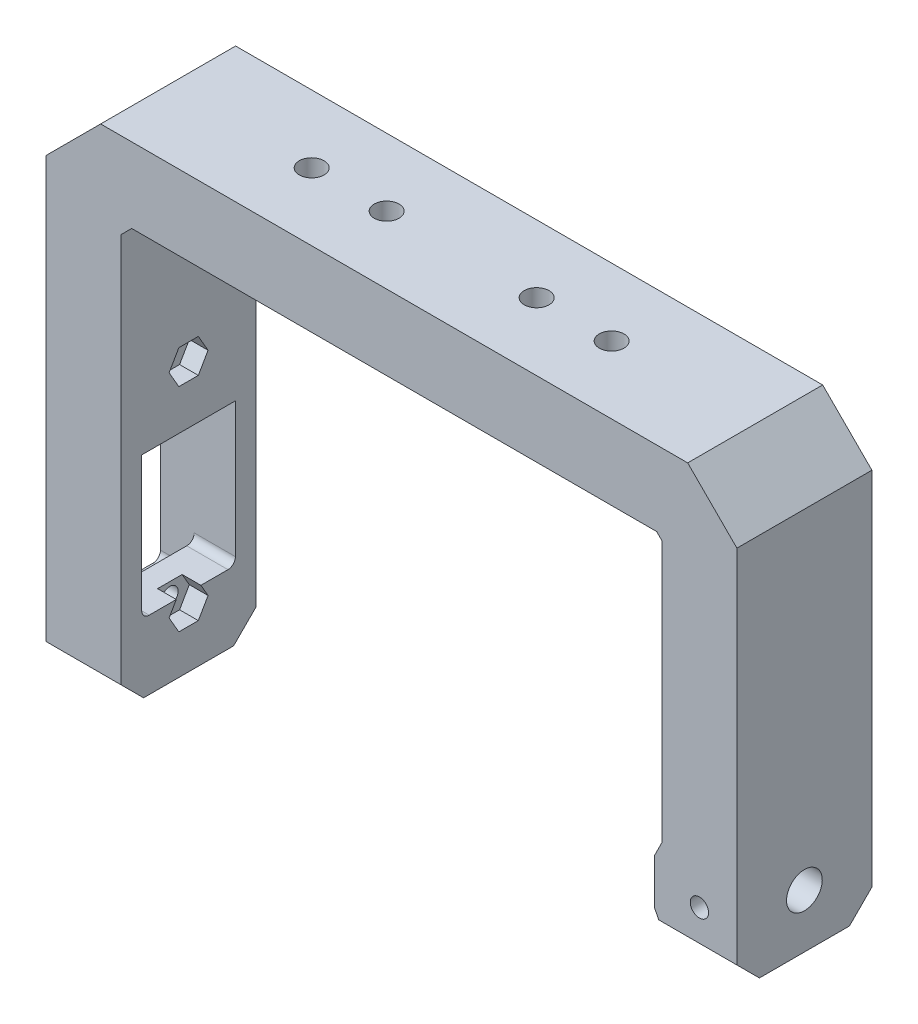
SolidWorks part; units mm, degrees
ref_plane "Front" through (0, 0, 0) normal (0, 0, 1) x (1, 0, 0)
ref_plane "Top" through (0, 0, 0) normal (0, 1, 0) x (1, 0, 0)
ref_plane "Right" through (0, 0, 0) normal (1, 0, 0) x (0, 0, -1)
sketch "Sketch1" plane through (0, 0, 0) normal (0, 0, 1) x (1, 0, 0)
  line L0 (-35, 0) -> (35, 0)
  line L1 (-35, 0) -> (-36.4142, -1.4142)
  line L2 (35, 0) -> (35.7071, -0.7071)
  line L3 (-36.4142, -1.4142) -> (-36.4142, -56.4142)
  line L4 (35.7071, -0.7071) -> (35.7071, -47.7071)
  line L5 (45.7071, 3.435) -> (45.7071, -47.7071)
  line L6 (39.1421, 10) -> (45.7071, 3.435)
  line L7 (-39.1421, 10) -> (39.1421, 10)
  line L8 (-39.1421, 10) -> (-46.4142, 2.7279)
  line L9 (-46.4142, 2.7279) -> (-46.4142, -56.4142)
  line L10 (-36.4142, -56.4142) -> (-46.4142, -56.4142)
  line L11 (35.7071, -47.7071) -> (45.7071, -47.7071)
  point P4 (0, 0)
  dimension "D1" = 70
  dimension "D2" = 2
  dimension "D3" = 1
  dimension "D4" = 55
  dimension "D5" = 47
  dimension "D6" = 45
  dimension "D7" = 10
extrude "Boss-Extrude1" add sketch "Sketch1" along normal mid plane 18
sketch "Sketch2" plane through (0, 10, 0) normal (0, 1, 0) x (1, 0, 0)
  line L0 (-39.1421, 0) -> (39.1421, 0) construction
  line L1 (39.1421, -9) -> (39.1421, 9) construction
  circle A0 centre (-10, 0) radius 0.5
  circle A1 centre (10, 0) radius 0.5
  circle A2 centre (-20, 0) radius 0.5
  circle A3 centre (20, 0) radius 0.5
  point P6 (0, 0)
  dimension "D1" = 1
  dimension "D2" = 1
  dimension "D5" = 1
  dimension "D6" = 1
  dimension "D3" = 10
  dimension "D4" = 10
  dimension "D7" = 20
  dimension "D8" = 20
extrude "Cut-Extrude1" cut sketch "Sketch2" against normal through all contours A0 | A1 | A2 | A3
sketch "Sketch9" plane through (45.7071, 0, 0) normal (1, 0, 0) x (0, 0, -1)
  line L0 (0, 0) -> (0, -47.7071) construction
  line L1 (-9, -47.7071) -> (9, -47.7071) construction
  line L4 (-9, 3.435) -> (9, 3.435) construction
  circle A0 centre (0, -40.565) radius 2.3812
  dimension "D1" = 44
  dimension "D2" = 4.7625
extrude "Pin Hole" cut sketch "Sketch9" against normal through all
sketch "Sketch20" plane through (0, 0, 0) normal (0, 0, 1) x (1, 0, 0)
  line L0 (35.7071, -40.565) -> (45.7071, -40.565) construction
  line L1 (35.7071, -38.1837) -> (35.7071, -42.9462) construction
  line L2 (45.7071, -42.9462) -> (45.7071, -38.1837) construction
  circle A0 centre (40.7071, -40.565) radius 1.2192
  dimension "D1" = 2.4385
extrude "spring pin" cut sketch "Sketch20" against normal through all both and the other way through all
sketch "Sketch32" plane through (-46.4142, 0, 0) normal (-1, 0, 0) x (0, 0, 1)
  line L0 (0, 2.7279) -> (0, -56.4142) construction
  line L1 (9, 2.7279) -> (-9, 2.7279) construction
  line L2 (9, -56.4142) -> (-9, -56.4142) construction
  line L8 (-6.25, -17.985) -> (6.25, -17.985)
  line L9 (-6.25, -17.985) -> (-6.25, -51.485)
  line L10 (-6.25, -51.485) -> (6.25, -51.485)
  line L11 (6.25, -17.985) -> (6.25, -51.485)
  line L12 (-6.25, -17.985) -> (6.25, -51.485) construction
  line L13 (-6.25, -51.485) -> (6.25, -17.985) construction
  point P6 (0, -34.735)
  point P11 (0, -40.565)
  dimension "D1" = 33.5
  dimension "D2" = 12.5
  dimension "D3" = 5.83
extrude "Cut-Extrude11" cut sketch "Sketch32" against normal blind 4.5
sketch "Sketch33" plane through (-41.9142, 0, 0) normal (-1, 0, 0) x (0, 0, 1)
  line L0 (0, -17.985) -> (0, -51.485) construction
  line L1 (6.25, -17.985) -> (-6.25, -17.985) construction
  line L2 (-6.25, -51.485) -> (6.25, -51.485) construction
  line L3 (6.25, -51.485) -> (6.25, -17.985) construction
  line L4 (-6.25, -22.235) -> (6.25, -22.235)
  line L5 (-6.25, -22.235) -> (-6.25, -47.235)
  line L6 (-6.25, -47.235) -> (6.25, -47.235)
  line L7 (6.25, -22.235) -> (6.25, -47.235)
  line L8 (-6.25, -22.235) -> (6.25, -47.235) construction
  line L9 (-6.25, -47.235) -> (6.25, -22.235) construction
  point P6 (0, -34.735)
  dimension "D1" = 25
extrude "Cut-Extrude12" cut sketch "Sketch33" against normal up to next
sketch "Sketch34" plane through (-41.9142, 0, 0) normal (-1, 0, 0) x (0, 0, 1)
  line L0 (0, -17.985) -> (0, -51.485) construction
  line L1 (6.25, -17.985) -> (-6.25, -17.985) construction
  line L2 (-6.25, -51.485) -> (6.25, -51.485) construction
  line L3 (-6.25, -21.0824) -> (6.25, -21.0824) construction
  line L4 (-6.25, -17.985) -> (-6.25, -22.235) construction
  line L5 (6.25, -22.235) -> (6.25, -17.985) construction
  line L6 (-6.25, -48.3874) -> (6.25, -48.3874) construction
  line L7 (-6.25, -47.235) -> (-6.25, -51.485) construction
  line L8 (6.25, -51.485) -> (6.25, -17.985) construction
  circle A0 centre (0, -20.5744) radius 1.1
  circle A3 centre (0, -48.8954) radius 1.1
  point P30 (0, -34.735)
  dimension "D1" = 2.2
  dimension "D4" = 2.2
  dimension "D7" = 28.321
  dimension "D8" = 0.508
  dimension "D9" = 27.305
  dimension "D10" = 13.6526
extrude "Cut-Extrude13" cut sketch "Sketch34" against normal up to next
fillet "Fillet1" radius 1 8 edges at (-44.1642, -51.485, 6.25) (-39.1642, -47.235, 6.25) (-39.1642, -22.235, 6.25) (-44.1642, -17.985, 6.25) (-39.1642, -22.235, -6.25) (-44.1642, -17.985, -6.25) (-39.1642, -47.235, -6.25) (-44.1642, -51.485, -6.25)
hole_wizard "Tap Drill for M4x0.7 Tap1" positions "Sketch39" profile "Sketch40" hole size "M4x0.7" standard "ANSI Metric" end condition up to next
sketch "Sketch39" plane through (0, 10, 0) normal (0, 1, 0) x (1, 0, 0)
  point P0 (-20, 0)
  point P3 (20, 0)
  point P7 (-10, 0)
  point P10 (10, 0)
sketch "Sketch40" plane through (-20, 10, 0) normal (1, 0, 0) x (0, 0, 1)
  line L0 (0, 0) -> (0, 66.4142)
  line L1 (0, 66.4142) -> (1.65, 66.4142)
  line L2 (1.65, 66.4142) -> (1.65, 0)
  line L5 (1.65, 0) -> (0, 0)
  line L11 (0, -6.35) -> (0, 107.95) construction
  dimension "Thru Hole Dia." = 3.3
  dimension "Thru Hole Depth" = 66.4142
sketch "Sketch41" plane through (-36.4142, 0, 0) normal (1, 0, 0) x (0, 0, -1)
  line L0 (-6.25, -22.235) -> (6.25, -22.235)
  line L1 (6.25, -22.235) -> (6.25, -28.235)
  line L2 (6.25, -46.235) -> (6.25, -23.235) construction
  line L3 (6.25, -28.235) -> (-6.25, -28.235)
  line L4 (-6.25, -23.235) -> (-6.25, -46.235) construction
  line L5 (-6.25, -28.235) -> (-6.25, -22.235)
  line L7 (5.25, -22.235) -> (-5.25, -22.235) construction
  dimension "D1" = 6
extrude "Boss-Extrude4" add sketch "Sketch41" against normal blind 3.5
sketch "Sketch43" plane through (-36.4142, 0, 0) normal (1, 0, 0) x (0, 0, -1)
  line L0 (0, -20.5744) -> (0, -48.8954) construction
  line L2 (-1.299, -22.8244) -> (1.299, -22.8244)
  line L3 (1.299, -22.8244) -> (2.5981, -20.5744)
  line L4 (2.5981, -20.5744) -> (1.299, -18.3244)
  line L5 (1.299, -18.3244) -> (-1.299, -18.3244)
  line L6 (-1.299, -18.3244) -> (-2.5981, -20.5744)
  line L7 (-2.5981, -20.5744) -> (-1.299, -22.8244)
  line L8 (-1.299, -46.6454) -> (-2.5981, -48.8954)
  line L9 (-2.5981, -48.8954) -> (-1.299, -51.1454)
  line L10 (-1.299, -51.1454) -> (1.299, -51.1454)
  line L11 (1.299, -51.1454) -> (2.5981, -48.8954)
  line L12 (2.5981, -48.8954) -> (1.299, -46.6454)
  line L13 (1.299, -46.6454) -> (-1.299, -46.6454)
  circle A0 centre (0, -20.5744) radius 2.25 construction
  circle A1 centre (0, -48.8954) radius 2.25 construction
  dimension "D1" = 4.5
  dimension "D2" = 4.5
extrude "Cut-Extrude14" cut sketch "Sketch43" against normal blind 2.5
sketch "Sketch44" plane through (0, 0, 0) normal (0, 0, 1) x (1, 0, 0)
  line L0 (45.7071, -40.565) -> (27.1965, -40.565) construction
  line L1 (45.7071, -42.9462) -> (45.7071, -38.1837) construction
  line L2 (34.7071, -43.565) -> (34.7071, -37.565)
  line L3 (34.7071, -37.565) -> (35.7071, -35.565)
  line L4 (35.7071, -0.7071) -> (35.7071, -47.7071) construction
  line L5 (35.7071, -35.565) -> (35.7071, -45.565)
  line L6 (35.7071, -38.1837) -> (35.7071, -42.9462) construction
  line L7 (34.7071, -40.565) -> (35.7071, -40.565)
  line L8 (34.7071, -43.565) -> (35.7071, -45.565)
  dimension "D1" = 6
  dimension "D2" = 10
  dimension "D3" = 1
extrude "Boss-Extrude6" add sketch "Sketch44" along normal mid plane 18 contours L2 L7 L5 L3 | L2 L8 L5 L7
chamfer "Chamfer1" distance 3 angle 45 4 edges at (40.7071, -47.7071, -9) (40.7071, -47.7071, 9) (-41.4142, -56.4142, -9) (-41.4142, -56.4142, 9)
sketch "Sketch45" plane through (35.7071, 0, 0) normal (1, 0, 0) x (0, 0, -1)
  circle A0 centre (0, -40.565) radius 2.3812
extrude "Cut-Extrude15" cut sketch "Sketch45" against normal up to next
sketch "Sketch46" plane through (0, 0, 9) normal (0, 0, 1) x (1, 0, 0)
  line L0 (-46.4142, -35) -> (-36.4142, -35) construction
  line L1 (-46.4142, 2.7279) -> (-46.4142, -53.4142) construction
  line L2 (-36.4142, -53.4142) -> (-36.4142, -1.4142) construction
  line L3 (-35, 0) -> (35, 0) construction
  line L4 (-46.4142, -30) -> (-36.4142, -30)
  line L5 (-46.4142, -30) -> (-46.4142, -40)
  line L6 (-46.4142, -40) -> (-36.4142, -40)
  line L7 (-36.4142, -30) -> (-36.4142, -40)
  line L8 (-46.4142, -30) -> (-36.4142, -40) construction
  line L9 (-46.4142, -40) -> (-36.4142, -30) construction
  point P6 (-41.4142, -35)
  dimension "D1" = 35
  dimension "D2" = 10
  dimension "D3" = 10
extrude "Boss-Extrude7" [suppressed] add sketch "Sketch46" along normal blind 4.5
sketch "Sketch47" [suppressed] plane through (0, -40, 0) normal (0, -1, 0) x (1, 0, 0)
  line L0 (-41.4142, 13.5) -> (-41.4142, 9) construction
  line L1 (-46.4142, 13.5) -> (-36.4142, 13.5) construction
  line L2 (-46.4142, 9) -> (-36.4142, 9) construction
  line L4 (-44.9142, 9) -> (-37.9142, 9)
  line L5 (-44.9142, 9) -> (-44.9142, 12.75)
  line L6 (-44.9142, 12.75) -> (-37.9142, 12.75)
  line L7 (-37.9142, 9) -> (-37.9142, 12.75)
  point P10 (-41.4142, 9)
  dimension "D1" = 7
  dimension "D2" = 3.75
extrude "Cut-Extrude16" [suppressed] cut sketch "Sketch47" against normal up to next
sketch "Sketch48" [suppressed] plane through (0, 0, 9) normal (0, 0, 1) x (1, 0, 0)
  line L0 (-46.4142, -12) -> (-36.4142, -12) construction
  line L1 (-46.4142, 2.7279) -> (-46.4142, -30) construction
  line L2 (-36.4142, -53.4142) -> (-36.4142, -40) construction
  line L3 (-35, 0) -> (35, 0) construction
  line L4 (-36.4142, -40) -> (-36.4142, -53.4142) construction
  line L5 (-46.4142, -7) -> (-36.4142, -7)
  line L6 (-46.4142, -7) -> (-46.4142, -17)
  line L7 (-46.4142, -17) -> (-36.4142, -17)
  line L8 (-36.4142, -7) -> (-36.4142, -17)
  line L9 (-46.4142, -7) -> (-36.4142, -17) construction
  line L10 (-46.4142, -17) -> (-36.4142, -7) construction
  point P8 (-41.4142, -12)
  dimension "D1" = 12
  dimension "D2" = 10
extrude "Boss-Extrude8" [suppressed] add sketch "Sketch48" along normal blind 4.5
sketch "Sketch49" [suppressed] plane through (0, -17, 0) normal (0, -1, 0) x (1, 0, 0)
  line L0 (-41.4142, 13.5) -> (-41.4142, 9) construction
  line L1 (-46.4142, 13.5) -> (-36.4142, 13.5) construction
  line L2 (-46.4142, 9) -> (-36.4142, 9) construction
  line L4 (-37.9142, 12.75) -> (-44.9142, 12.75)
  line L5 (-37.9142, 12.75) -> (-37.9142, 9)
  line L6 (-37.9142, 9) -> (-44.9142, 9)
  line L7 (-44.9142, 12.75) -> (-44.9142, 9)
extrude "Cut-Extrude17" [suppressed] cut sketch "Sketch49" against normal up to next
